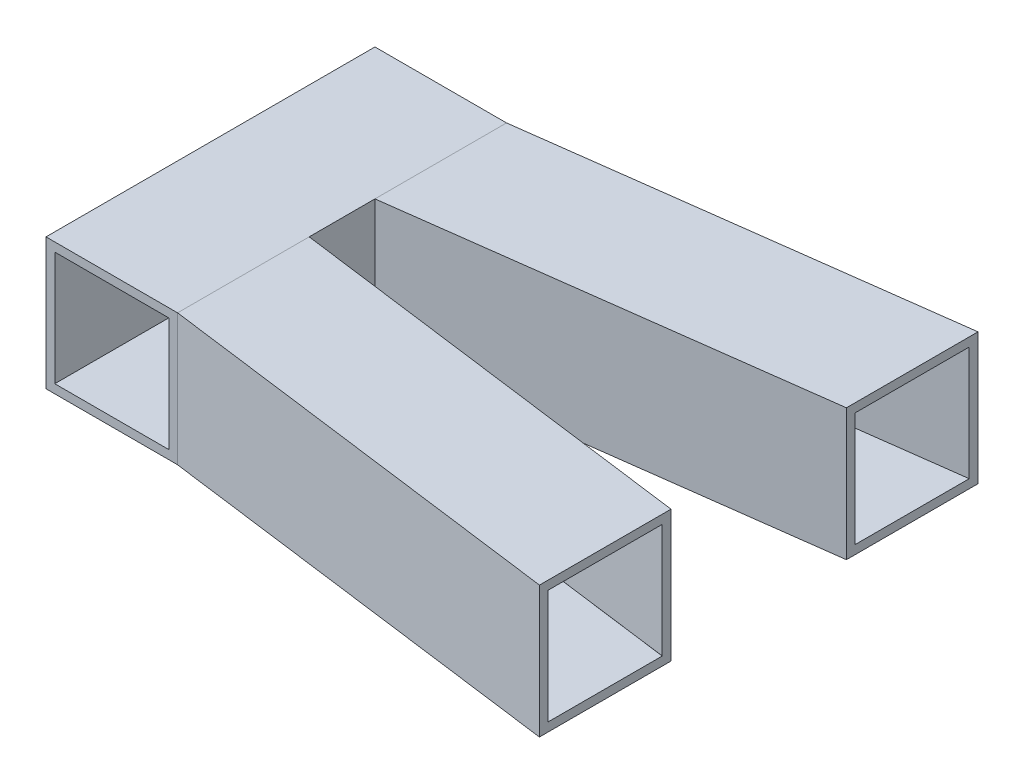
SolidWorks part; units mm, degrees
ref_plane "Płaszczyzna przednia" through (0, 0, 0) normal (0, 0, 1) x (1, 0, 0)
ref_plane "Płaszczyzna górna" through (0, 0, 0) normal (0, 1, 0) x (1, 0, 0)
ref_plane "Płaszczyzna prawa" through (0, 0, 0) normal (1, 0, 0) x (0, 0, -1)
sketch "Szkic1" plane through (0, 0, 0) normal (0, 0, 1) x (1, 0, 0)
  line L0 (-26, 26) -> (26, 26)
  line L1 (-30, -30) -> (30, -30)
  line L2 (-30, -30) -> (-30, 30)
  line L3 (-30, 30) -> (30, 30)
  line L4 (30, -30) -> (30, 30)
  line L5 (-30, -30) -> (30, 30) construction
  line L6 (-30, 30) -> (30, -30) construction
  line L7 (26, -26) -> (26, 26)
  line L8 (-26, -26) -> (26, -26)
  line L9 (-26, -26) -> (-26, 26)
  point P0 (0, 0)
  dimension "D1" = 60
  dimension "D2" = 60
  dimension "D3" = 4
extrude "Dodanie-wyciągnięcie1" add sketch "Szkic1" along normal mid plane 150
sketch "Szkic2" plane through (30, 0, 0) normal (1, 0, 0) x (0, 0, -1)
  line L0 (-75, -30) -> (75, -30) construction
  line L1 (-75, 30) -> (-15, 30)
  line L2 (-75, 30) -> (-75, -30)
  line L3 (-75, -30) -> (-15, -30)
  line L4 (-15, 30) -> (-15, -30)
  line L5 (-71, 26) -> (-19, 26)
  line L6 (75, 30) -> (15, 30)
  line L7 (75, 30) -> (75, -30)
  line L8 (75, -30) -> (15, -30)
  line L9 (15, 30) -> (15, -30)
  line L10 (-19, 26) -> (-19, -26)
  line L11 (-71, -26) -> (-19, -26)
  line L12 (-71, 26) -> (-71, -26)
  line L13 (71, 26) -> (19, 26)
  line L14 (19, 26) -> (19, -26)
  line L15 (71, -26) -> (19, -26)
  line L16 (71, 26) -> (71, -26)
  dimension "D1" = 60
  dimension "D2" = 60
  dimension "D3" = 4
ref_plane "Płaszczyzna1" through (220, 0, 0) normal (1, 0, 0) x (0, 0, -1)
sketch "Szkic3" plane through (220, 0, 0) normal (1, 0, 0) x (0, 0, -1)
  line L0 (75, -30) -> (15, -30) construction
  line L1 (-100, 29.9682) -> (-40, 29.9682)
  line L2 (-100, 29.9682) -> (-100, -30.0318)
  line L3 (-100, -30.0318) -> (-40, -30.0318)
  line L4 (-40, 29.9682) -> (-40, -30.0318)
  line L5 (100, 30) -> (40, 30)
  line L6 (100, 30) -> (100, -30)
  line L7 (100, -30) -> (40, -30)
  line L8 (40, 30) -> (40, -30)
  line L9 (0, 33) -> (0, -33) construction
  line L10 (-96, 25.9682) -> (-44, 25.9682)
  line L11 (-44, 25.9682) -> (-44, -26.0318)
  line L12 (-96, -26.0318) -> (-44, -26.0318)
  line L13 (-96, 25.9682) -> (-96, -26.0318)
  line L14 (96, 26) -> (44, 26)
  line L15 (44, 26) -> (44, -26)
  line L16 (96, -26) -> (44, -26)
  line L17 (96, 26) -> (96, -26)
  point P20 (0, 0)
  dimension "D1" = 60
  dimension "D2" = 60
  dimension "D3" = 60
  dimension "D4" = 60
  dimension "D5" = 40
  dimension "D6" = 40
  dimension "D7" = 4
surface "Powierzchnia-Płaszczyzna1" sketch "Szkic3"
ref_plane "Płaszczyzna2" through (-1.4295, 0, 10.8645) normal (-0.1305, 0, 0.9915) x (0.9915, 0, 0.1305)
sketch "Szkic4" plane through (-1.4295, 0, 10.8645) normal (-0.1305, 0, 0.9915) x (0.9915, 0, 0.1305)
  line L1 (223.3381, 29.9682) -> (31.7004, 29.9682)
  line L2 (223.3381, 29.9682) -> (223.3381, -30)
  line L3 (223.3381, -30) -> (31.7004, -30)
  line L4 (31.7004, 29.9682) -> (31.7004, -30)
surface "Powierzchnia-wypełnij1" sketch "Szkic4"
ref_plane "Płaszczyzna4" through (-1.9469, 0, 14.7965) normal (0.1305, 0, -0.9915) x (-0.9915, 0, -0.1305)
sketch "Szkic6" plane through (-1.9469, 0, 14.7965) normal (0.1305, 0, -0.9915) x (-0.9915, 0, -0.1305)
  line L1 (-223.8599, 25.9682) -> (-32.2223, 25.9682)
  line L2 (-223.8599, 25.9682) -> (-223.8599, -26)
  line L3 (-223.8599, -26) -> (-32.2223, -26)
  line L4 (-32.2223, 25.9682) -> (-32.2223, -26)
surface "Powierzchnia-Płaszczyzna2" sketch "Szkic6"
ref_plane "Płaszczyzna5" through (0.0044, 26.005, 0) normal (-0.0002, -1, 0) x (-1, 0.0002, 0)
sketch "Szkic7" plane through (0.0044, 26.005, 0) normal (-0.0002, -1, 0) x (-1, 0.0002, 0)
  line L0 (-29.9956, -19) -> (-219.9956, -44)
  line L1 (-219.9956, -44) -> (-219.9956, -96)
  line L2 (-219.9956, -96) -> (-29.9956, -71)
  line L3 (-29.9956, -71) -> (-29.9956, -19)
surface "Powierzchnia-Płaszczyzna3" sketch "Szkic7"
ref_plane "Płaszczyzna6" through (-8.6726, 0, 65.9115) normal (-0.1305, 0, 0.9915) x (0.9915, 0, 0.1305)
sketch "Szkic8" plane through (-8.6726, 0, 65.9115) normal (-0.1305, 0, 0.9915) x (0.9915, 0, 0.1305)
  line L1 (39.0059, 26) -> (230.6436, 26)
  line L2 (39.0059, 26) -> (39.0059, -26.0318)
  line L3 (39.0059, -26.0318) -> (230.6436, -26.0318)
  line L4 (230.6436, 26) -> (230.6436, -26.0318)
surface "Powierzchnia-Płaszczyzna4" sketch "Szkic8"
ref_plane "Płaszczyzna7" through (-0.0044, -25.995, 0) normal (-0.0002, -1, 0) x (-1, 0.0002, 0)
sketch "Szkic9" plane through (-0.0044, -25.995, 0) normal (-0.0002, -1, 0) x (-1, 0.0002, 0)
  line L0 (-29.9956, -71) -> (-220.0044, -96)
  line L1 (-29.9956, -71) -> (-29.9956, -19) construction
  line L2 (-220.0044, -96) -> (-220.0044, -44)
  line L3 (-220.0044, -44) -> (-30.0044, -19)
  line L4 (-30.0044, -19) -> (-29.9956, -71)
surface "Powierzchnia-Płaszczyzna5" sketch "Szkic9"
ref_plane "Płaszczyzna8" through (0.005, 30.005, 0) normal (-0.0002, -1, 0) x (-1, 0.0002, 0)
sketch "Szkic10" plane through (0.005, 30.005, 0) normal (-0.0002, -1, 0) x (-1, 0.0002, 0)
  line L0 (-29.995, -15) -> (-219.995, -40)
  line L1 (-219.995, -40) -> (-219.995, -100)
  line L2 (-219.995, -100) -> (-29.995, -75)
  line L3 (-29.995, -75) -> (-29.995, -15)
surface "Powierzchnia-Płaszczyzna6" sketch "Szkic10"
ref_plane "Płaszczyzna9" through (-9.1899, 0, 69.8434) normal (-0.1305, 0, 0.9915) x (0.9915, 0, 0.1305)
sketch "Szkic11" plane through (-9.1899, 0, 69.8434) normal (-0.1305, 0, 0.9915) x (0.9915, 0, 0.1305)
  line L1 (39.5277, 30) -> (231.1654, 30)
  line L2 (39.5277, 30) -> (39.5277, -30.0318)
  line L3 (39.5277, -30.0318) -> (231.1654, -30.0318)
  line L4 (231.1654, 30) -> (231.1654, -30.0318)
surface "Powierzchnia-Płaszczyzna7" sketch "Szkic11"
ref_plane "Płaszczyzna10" through (-0.005, -29.995, 0) normal (-0.0002, -1, 0) x (-1, 0.0002, 0)
sketch "Szkic12" plane through (-0.005, -29.995, 0) normal (-0.0002, -1, 0) x (-1, 0.0002, 0)
  line L0 (-220.005, -100) -> (-220.005, -40)
  line L1 (-220.005, -40) -> (-30.005, -15)
  line L2 (-30.005, -15) -> (-30.005, -75)
  line L3 (-30.005, -75) -> (-220.005, -100)
surface "Powierzchnia-Płaszczyzna8" sketch "Szkic12"
surface "Powierzchnia-Wyciągnięcie po profilach1"
sketch "Szkic22" plane through (0, 30, 0) normal (0, 1, 0) x (1, 0, 0)
  line L0 (30, 75) -> (220, 100)
  line L1 (220, 100) -> (220, 40)
  line L2 (220, 40) -> (30, 15)
  line L3 (30, -75) -> (30, 75) construction
  line L4 (30, 15) -> (30, 75)
surface "Powierzchnia-Płaszczyzna9" sketch "Szkic22"
sketch "Szkic23" plane through (0, -30, 0) normal (0, -1, 0) x (1, 0, 0)
  line L0 (30, -75) -> (220, -100)
  line L1 (220, -100) -> (220, -40)
  line L2 (220, -40) -> (30, -15)
  line L3 (30, 75) -> (30, -75) construction
  line L4 (30, -15) -> (30, -75)
surface "Powierzchnia-Płaszczyzna10" sketch "Szkic23"
ref_plane "Płaszczyzna12" through (-1.4295, 0, -10.8645) normal (-0.1305, 0, -0.9915) x (-0.9915, 0, 0.1305)
sketch "Szkic24" plane through (-1.4295, 0, -10.8645) normal (-0.1305, 0, -0.9915) x (-0.9915, 0, 0.1305)
  line L1 (-31.7004, 30) -> (-223.3381, 30)
  line L2 (-31.7004, 30) -> (-31.7004, -30)
  line L3 (-31.7004, -30) -> (-223.3381, -30)
  line L4 (-223.3381, 30) -> (-223.3381, -30)
surface "Powierzchnia-Płaszczyzna11" sketch "Szkic24"
ref_plane "Płaszczyzna14" through (-9.1899, 0, -69.8434) normal (0.1305, 0, 0.9915) x (0.9915, 0, -0.1305)
sketch "Szkic26" plane through (-9.1899, 0, -69.8434) normal (0.1305, 0, 0.9915) x (0.9915, 0, -0.1305)
  line L1 (39.5277, -30) -> (231.1654, -30)
  line L2 (39.5277, -30) -> (39.5277, 30)
  line L3 (39.5277, 30) -> (231.1654, 30)
  line L4 (231.1654, -30) -> (231.1654, 30)
surface "Powierzchnia-Płaszczyzna12" sketch "Szkic26"
sketch "Szkic28" plane through (-30, 0, 0) normal (-1, 0, 0) x (0, 0, 1)
  circle A0 centre (0, 0) radius 5
  dimension "D1" = 10
extrude "Wytnij-wyciągnięcie1" cut sketch "Szkic28" against normal blind 25
